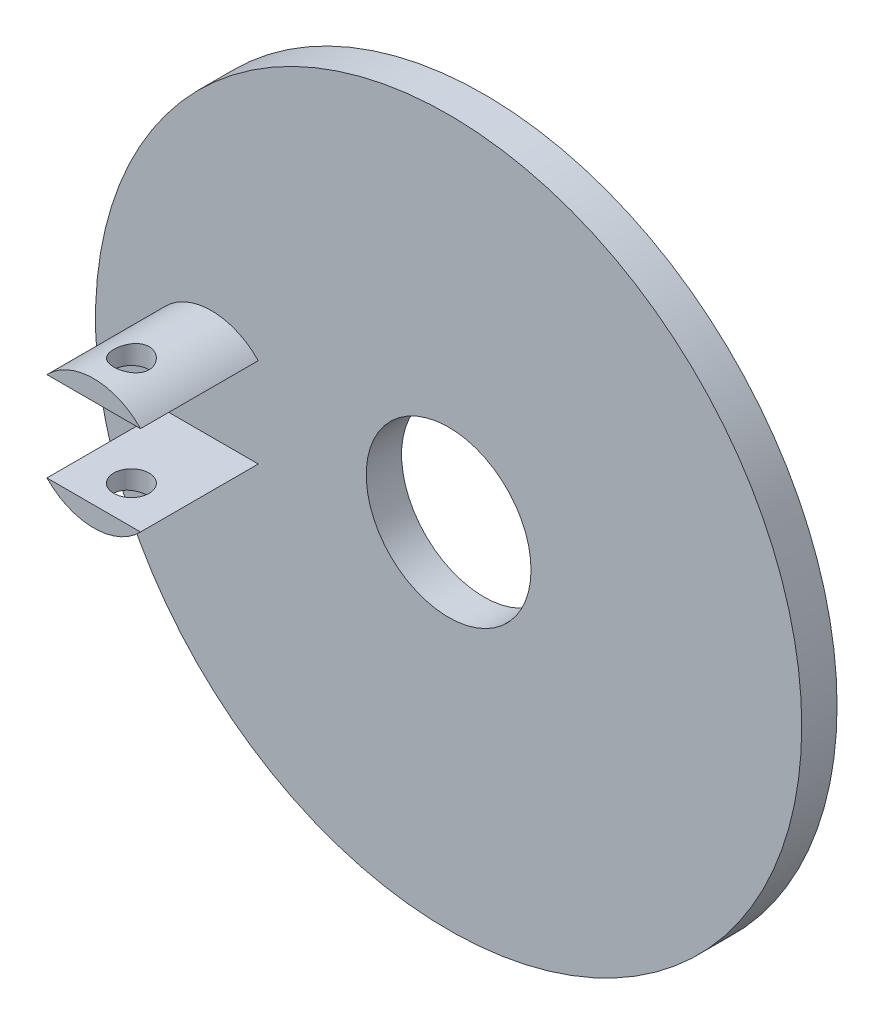
SolidWorks part; units mm, degrees
ref_plane "Front Plane" through (0, 0, 0) normal (0, 0, 1) x (1, 0, 0)
ref_plane "Top Plane" through (0, 0, 0) normal (0, 1, 0) x (1, 0, 0)
ref_plane "Right Plane" through (0, 0, 0) normal (1, 0, 0) x (0, 0, -1)
sketch "Sketch1" plane through (0, 0, 0) normal (0, 0, 1) x (1, 0, 0)
  circle A0 centre (0, 0) radius 75
  circle A1 centre (0, 0) radius 17.5
  dimension "D1" = 35
  dimension "D2" = 150
extrude "Boss-Extrude2" add sketch "Sketch1" along normal blind 7.5
sketch "Sketch2" plane through (0, 0, 7.5) normal (0, 0, 1) x (1, 0, 0)
  circle A0 centre (-50.3744, 0) radius 13.75
  dimension "D1" = 27.5
extrude "Boss-Extrude3" add sketch "Sketch2" along normal blind 25 contours A0
sketch "Sketch3" plane through (0, 0, 32.5) normal (0, 0, 1) x (1, 0, 0)
  line L2 (-60.3149, 9.5) -> (-40.434, 9.5)
  line L3 (-60.3149, -9.5) -> (-40.434, -9.5)
  arc A1 (-40.434, 9.5) -> (-60.3149, 9.5) centre (-50.3744, 0) ccw
  circle A3 centre (-50.3744, 0) radius 13.75
  arc A4 (-60.3149, -9.5) -> (-40.434, -9.5) centre (-50.3744, 0) ccw
  dimension "D2" = 19
  dimension "D1" = 0
extrude "Cut-Extrude3" cut sketch "Sketch3" against normal up to surface (25 mm away) flip side to cut up to face at (-36.6244, 0, 7.5)
sketch "Sketch6" plane through (0, -9.5, 0) normal (0, 1, 0) x (1, 0, 0)
  line L0 (-60.3149, -32.5) -> (-40.434, -32.5) construction
  circle A0 centre (-50.3744, -24.5) radius 3.75
  point P4 (-50.3744, -32.5)
  dimension "D1" = 7.5
  dimension "D2" = 8
extrude "Cut-Extrude4" cut sketch "Sketch6" against normal through all both and the other way through all
